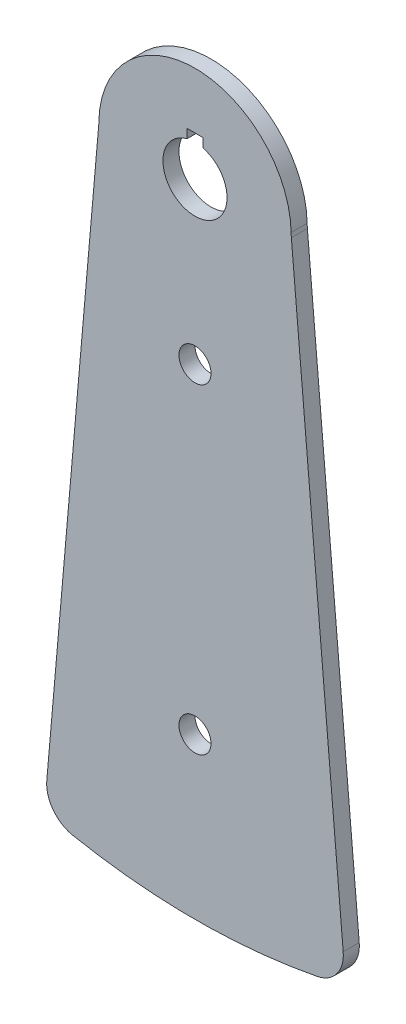
SolidWorks part; units mm, degrees
material "AISI 1020"
ref_plane "Front Plane" through (0, 0, 0) normal (0, 0, 1) x (1, 0, 0)
ref_plane "Top Plane" through (0, 0, 0) normal (0, 1, 0) x (1, 0, 0)
ref_plane "Right Plane" through (0, 0, 0) normal (1, 0, 0) x (0, 0, -1)
sketch "Sketch1" plane through (0, 0, 0) normal (0, 0, 1) x (1, 0, 0)
  line L0 (-59.6996, -246.8845) -> (-38.1844, -0.9642)
  line L1 (-38.1, 0) -> (38.1, 0) construction
  line L2 (38.1844, -0.9642) -> (59.6996, -246.8845)
  line L3 (0, 0) -> (-117.3327, -48.6008) construction
  line L4 (0, 0) -> (0, -254) construction
  line L5 (117.3327, -48.6008) -> (0, 0) construction
  arc A0 (-59.6996, -246.8845) -> (59.6996, -246.8845) centre (0, 0) ccw
  circle A1 centre (0, 0) radius 127 construction
  circle A2 centre (0, 0) radius 12.7
  arc A3 (38.0926, 0.7497) -> (-38.0926, 0.7497) centre (0, 0) ccw
  circle A4 centre (-117.3327, -48.6008) radius 12.7 construction
  circle A5 centre (117.3327, -48.6008) radius 12.7 construction
  arc A6 (38.1844, -0.9642) -> (38.0926, 0.7497) centre (63.4877, 1.2495) cw
  arc A7 (-38.1844, -0.9642) -> (-38.0926, 0.7497) centre (-63.4877, 1.2495) ccw
  dimension "D1" = 508
  dimension "D2" = 254
  dimension "D3" = 25.4
  dimension "D4" = 25.4
  dimension "D5" = 25.4
  dimension "D8" = 25.4
  dimension "D6" = 135
  dimension "D7" = 67.5
  dimension "D9" = 10
extrude "Boss-Extrude1" add sketch "Sketch1" along normal mid plane 6.35
sketch "Sketch8" plane through (0, 0, 0) normal (0, 0, 1) x (1, 0, 0)
  line L0 (0, 0) -> (0, 12.7) construction
  line L2 (3.175, 9.525) -> (-3.175, 9.525)
  line L3 (3.175, 9.525) -> (3.175, 15.875)
  line L4 (3.175, 15.875) -> (-3.175, 15.875)
  line L5 (-3.175, 9.525) -> (-3.175, 15.875)
  line L6 (3.175, 9.525) -> (-3.175, 15.875) construction
  line L7 (3.175, 15.875) -> (-3.175, 9.525) construction
  arc A1 (3.175, 12.2967) -> (-3.175, 12.2967) centre (0, 0) ccw
  point P1 (0, 9.8173)
  point P2 (0, 0)
  point P11 (0, 0)
  dimension "D3" = 12.7
  dimension "D1" = 6.35
  dimension "D2" = 6.35
extrude "Cut-Extrude1" cut sketch "Sketch8" against normal through all both and the other way through all contours L3 L4 L5 L2
sketch "Sketch9" plane through (0, 0, 0) normal (0, 0, 1) x (1, 0, 0)
  line L0 (0, 0) -> (0, -254) construction
  circle A0 centre (0, -63.5) radius 6.35
  circle A1 centre (0, -190.5) radius 6.35
  arc A2 (-59.6996, -246.8845) -> (59.6996, -246.8845) centre (0, 0) ccw construction
  point P7 (0, -254)
  dimension "D1" = 12.7
  dimension "D2" = 127
  dimension "D3" = 63.5
extrude "Cut-Extrude2" cut sketch "Sketch9" against normal through all both and the other way through all
fillet "Fillet1" radius 12.7 2 edges at (59.6996, -246.8845, 0) (-59.6996, -246.8845, 0)
